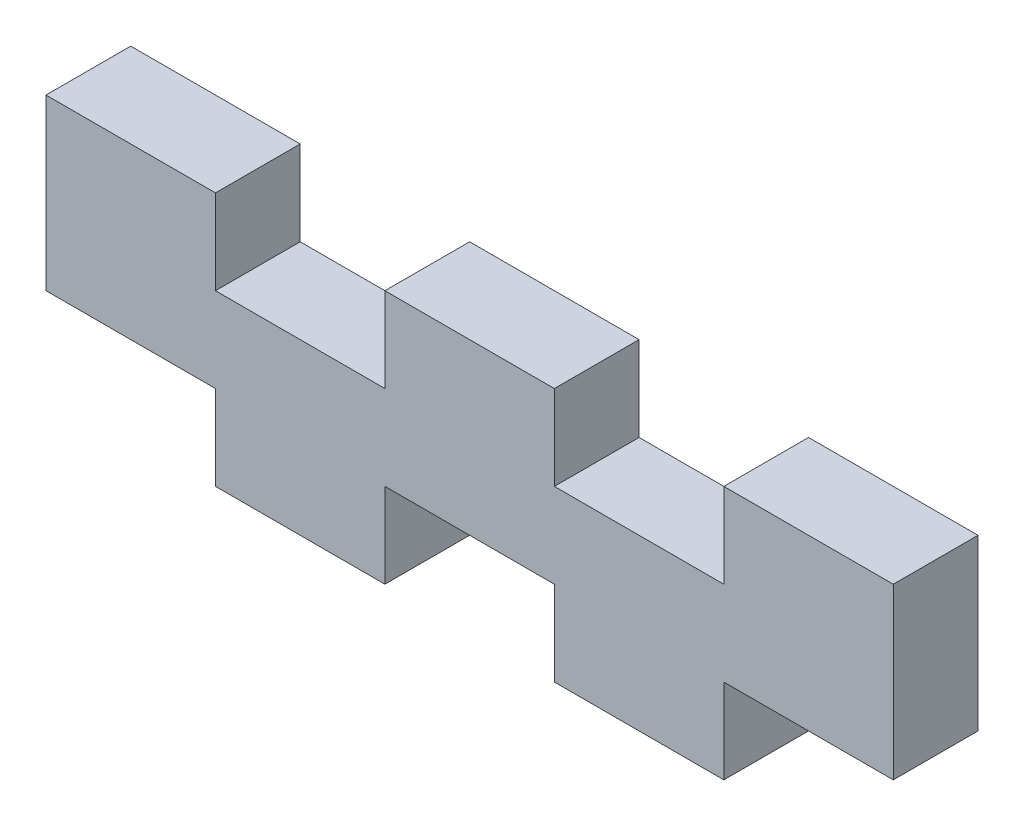
SolidWorks part; units mm, degrees
ref_plane "Front Plane" through (0, 0, 0) normal (0, 0, 1) x (1, 0, 0)
ref_plane "Top Plane" through (0, 0, 0) normal (0, 1, 0) x (1, 0, 0)
ref_plane "Right Plane" through (0, 0, 0) normal (1, 0, 0) x (0, 0, -1)
sketch "Sketch1" plane through (0, 0, 0) normal (0, 0, 1) x (1, 0, 0)
  line L1 (0, 0) -> (50.8, 0)
  line L2 (0, 0) -> (0, 15.24)
  line L3 (0, 15.24) -> (50.8, 15.24)
  line L4 (50.8, 0) -> (50.8, 15.24)
  dimension "D1" = 15.24
  dimension "D2" = 50.8
extrude "Boss-Extrude1" add sketch "Sketch1" along normal blind 5.08
sketch "Sketch3" plane through (0, 0, 0) normal (0, 0, -1) x (-1, 0, 0)
  line L0 (0, 0) -> (-50.8, 0) construction
  line L1 (0, 0) -> (-10.16, 0)
  line L2 (0, 0) -> (0, 5.08)
  line L3 (0, 5.08) -> (-10.16, 5.08)
  line L4 (-10.16, 0) -> (-10.16, 5.08)
  line L5 (-20.32, 0) -> (-30.48, 0)
  line L6 (-20.32, 0) -> (-20.32, 5.08)
  line L7 (-20.32, 5.08) -> (-30.48, 5.08)
  line L8 (-30.48, 0) -> (-30.48, 5.08)
  line L9 (-10.16, 5.08) -> (-20.32, 5.08) construction
  line L10 (-50.8, 0) -> (-40.64, 0)
  line L11 (-50.8, 0) -> (-50.8, 5.08)
  line L12 (-50.8, 5.08) -> (-40.64, 5.08)
  line L13 (-40.64, 0) -> (-40.64, 5.08)
  line L14 (-30.48, 5.08) -> (-40.64, 5.08) construction
  dimension "D1" = 5.08
extrude "Cut-Extrude2" cut sketch "Sketch3" against normal up to next
sketch "Sketch4" plane through (0, 0, 5.08) normal (0, 0, 1) x (1, 0, 0)
  line L0 (50.8, 15.24) -> (0, 15.24) construction
  line L1 (10.16, 15.24) -> (20.32, 15.24)
  line L2 (10.16, 15.24) -> (10.16, 10.16)
  line L3 (10.16, 10.16) -> (20.32, 10.16)
  line L4 (20.32, 15.24) -> (20.32, 10.16)
  line L5 (-9.525, 10.16) -> (0, 10.16) construction
  line L6 (10.16, 10.16) -> (0, 10.16) construction
  line L7 (30.48, 15.24) -> (40.64, 15.24)
  line L8 (30.48, 15.24) -> (30.48, 10.16)
  line L9 (30.48, 10.16) -> (40.64, 10.16)
  line L10 (40.64, 15.24) -> (40.64, 10.16)
  line L11 (0, 15.24) -> (0, 5.08) construction
  line L12 (20.32, 10.16) -> (30.48, 10.16) construction
  line L13 (40.64, 10.16) -> (50.8, 10.16) construction
  line L14 (50.8, 5.08) -> (50.8, 15.24) construction
extrude "Cut-Extrude3" cut sketch "Sketch4" against normal up to next
equation "\"Foamcore\"= 0.2in"
equation "\"MDF\"= 0.2in"
equation "\"D1@Sketch1\"=3*\"MDF\""
equation "\"D1@Boss-Extrude1\"=\"MDF\""
equation "\"D1@Sketch3\"=\"MDF\""
